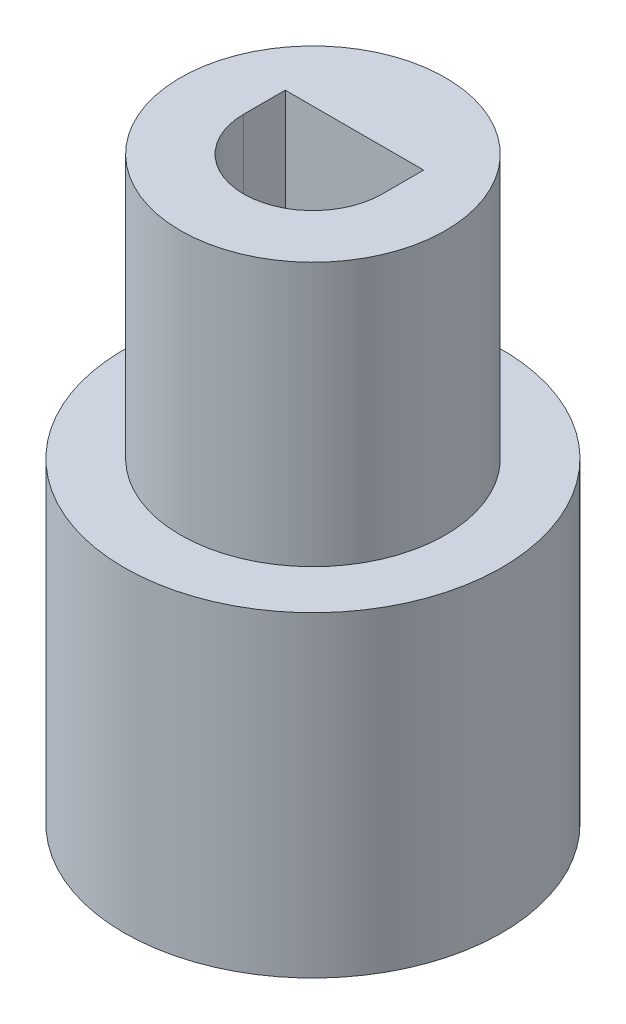
SolidWorks part; units mm, degrees
ref_plane "Front Plane" through (0, 0, 0) normal (0, 0, 1) x (1, 0, 0)
ref_plane "Top Plane" through (0, 0, 0) normal (0, 1, 0) x (1, 0, 0)
ref_plane "Right Plane" through (0, 0, 0) normal (1, 0, 0) x (0, 0, -1)
sketch "Sketch1" plane through (0, 0, 0) normal (0, 1, 0) x (1, 0, 0)
  circle A0 centre (0, 0) radius 4.7625
  circle A1 centre (0, 0) radius 7.1625
  dimension "D1" = 9.525
  dimension "D2" = 2.4
extrude "Boss-Extrude1" add sketch "Sketch1" along normal blind 10 contours A1 A0
sketch "Sketch2" plane through (0, 10, 0) normal (0, 1, 0) x (1, 0, 0)
  circle A0 centre (0, 0) radius 4.7625 construction
  circle A1 centre (0, 0) radius 4.7625
  circle A3 centre (0, 0) radius 7.1625
  circle A4 centre (0, 0) radius 7.1625
  circle M1 centre (0, 0) radius 4.7625
  circle M2 centre (0, 0) radius 7.1625
  dimension "D1" = 0
extrude "Boss-Extrude2" add sketch "Sketch2" along normal blind 2 contours M2 M1 | M1
sketch "Sketch3" plane through (0, 12, 0) normal (0, 1, 0) x (1, 0, 0)
  line L0 (-2.625, 0) -> (-2.625, 1.575)
  line L1 (-2.625, 1.575) -> (2.625, 1.575)
  line L2 (2.625, 1.575) -> (2.625, 0)
  arc A0 (-2.625, 0) -> (2.625, 0) centre (0, 0) ccw
  circle A1 centre (0, 0) radius 5.025
  point P1 (0, 0)
  dimension "D1" = 5.25
  dimension "D2" = 2.4
  dimension "D3" = 4.2
extrude "Boss-Extrude3" add sketch "Sketch3" along normal blind 10
